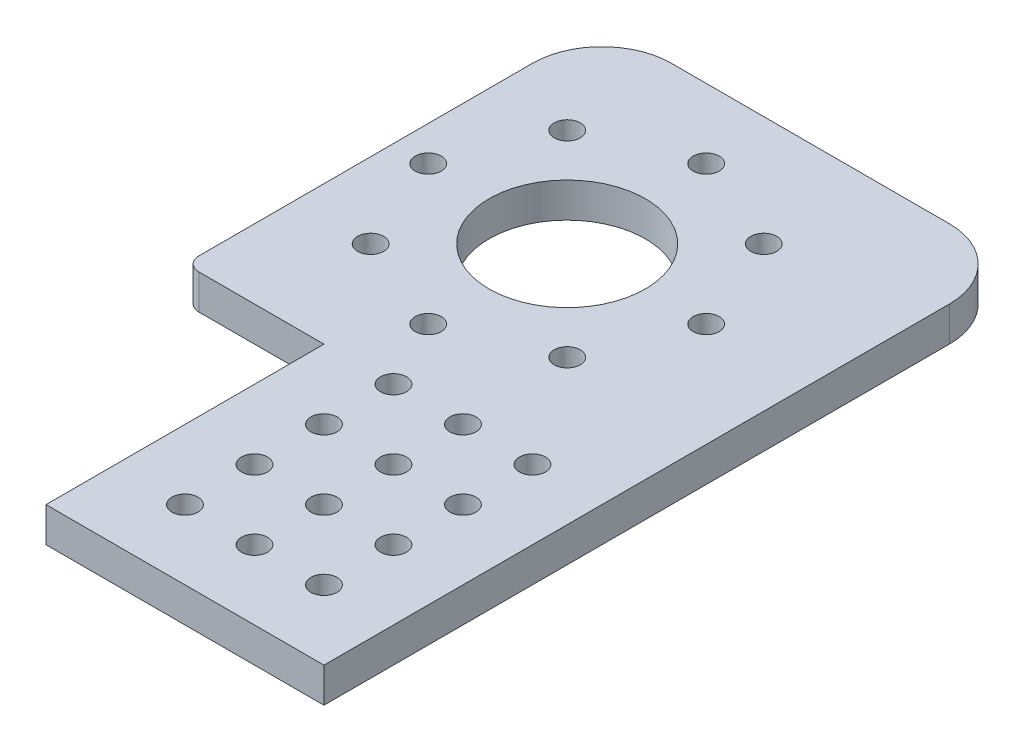
SolidWorks part; units mm, degrees
ref_plane "Front Plane" through (0, 0, 0) normal (0, 0, 1) x (1, 0, 0)
ref_plane "Top Plane" through (0, 0, 0) normal (0, 1, 0) x (1, 0, 0)
ref_plane "Right Plane" through (0, 0, 0) normal (1, 0, 0) x (0, 0, -1)
sketch "Sketch1" plane through (0, 0, 0) normal (0, 1, 0) x (1, 0, 0)
  line L1 (0, 0) -> (50.8, 0)
  line L2 (0, 0) -> (0, 50.8)
  line L3 (-25.4, 127) -> (50.8, 127)
  line L4 (50.8, 0) -> (50.8, 127)
  line L7 (0, 50.8) -> (-25.4, 50.8)
  line L8 (-25.4, 127) -> (-25.4, 50.8)
  circle A0 centre (12.7, 12.7) radius 2.3813
  circle A3 centre (25.4, 12.7) radius 2.3812
  circle A4 centre (38.1, 12.7) radius 2.3812
  circle A5 centre (25.4, 25.4) radius 2.3812
  circle A6 centre (38.1, 25.4) radius 2.3812
  circle A7 centre (25.4, 38.1) radius 2.3813
  circle A8 centre (38.1, 38.1) radius 2.3812
  circle A15 centre (12.7, 25.4) radius 2.3813
  circle A16 centre (12.7, 38.1) radius 2.3813
  circle A26 centre (6.35, 88.9) radius 14.2875
  circle A27 centre (12.7, 50.8) radius 2.3812
  circle A28 centre (25.4, 50.8) radius 2.3812
  circle A29 centre (38.1, 50.8) radius 2.3813
  dimension "D1" = 12.7
  dimension "D3" = 4.7625
  dimension "D4" = 3
  dimension "D11" = 28.575
  dimension "D7" = 127
  dimension "D2" = 12.7
  dimension "D6" = 12.7
  dimension "D8" = 12.7
  dimension "D9" = 12.7
  dimension "D10" = 50.8
  dimension "D12" = 38.1
  dimension "D13" = 31.75
  dimension "D14" = 25.4
  dimension "D5" = 4
extrude "Boss-Extrude1" add sketch "Sketch1" along normal blind 6.35
fillet "Fillet1" radius 12.7 2 edges at (-25.4, 3.175, -127) (50.8, 3.175, -127)
sketch "Sketch2" plane through (0, 6.35, 0) normal (0, 1, 0) x (1, 0, 0)
  line L0 (6.35, 88.9) -> (-19.05, 88.9) construction
  line L1 (6.35, 88.9) -> (-11.6105, 106.8605) construction
  circle A0 centre (6.35, 88.9) radius 25.4 construction
  circle A1 centre (-19.05, 88.9) radius 2.3813
  circle A2 centre (-11.6105, 106.8605) radius 2.3812
  circle A3 centre (6.35, 114.3) radius 2.3812
  circle A4 centre (24.3105, 106.8605) radius 2.3812
  circle A5 centre (31.75, 88.9) radius 2.3812
  circle A6 centre (24.3105, 70.9395) radius 2.3812
  circle A7 centre (6.35, 63.5) radius 2.3812
  circle A8 centre (-11.6105, 70.9395) radius 2.3812
  dimension "D1" = 50.8
  dimension "D2" = 4.7625
  dimension "D4" = 45
  dimension "D3" = 8
extrude "Cut-Extrude1" cut sketch "Sketch2" against normal through all
fillet "Fillet2" radius 2.54 1 edges at (-25.4, 3.175, -50.8)
